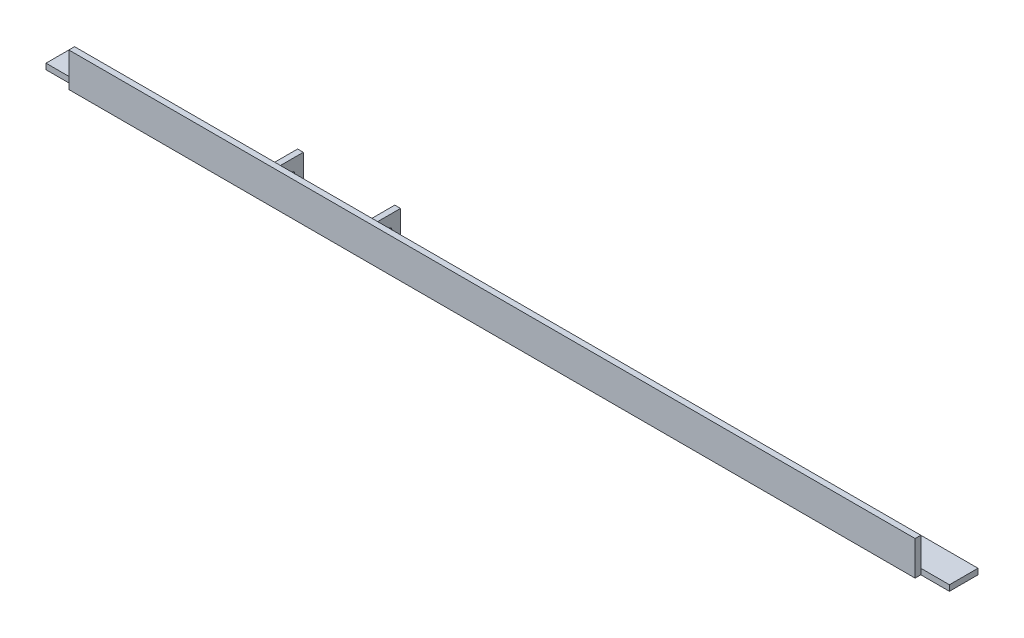
SolidWorks part; units mm, degrees
ref_plane "Front Plane" through (0, 0, 0) normal (0, 0, 1) x (1, 0, 0)
ref_plane "Top Plane" through (0, 0, 0) normal (0, 1, 0) x (1, 0, 0)
ref_plane "Right Plane" through (0, 0, 0) normal (1, 0, 0) x (0, 0, -1)
sketch "Sketch1" plane through (0, 0, 0) normal (1, 0, 0) x (0, 0, -1)
  line L0 (0, 0) -> (0, 31.75)
  line L1 (0, 31.75) -> (-6.35, 31.75)
  line L2 (-6.35, 31.75) -> (-6.35, -6.35)
  line L3 (-6.35, -6.35) -> (0, 0) construction
  line L4 (31.75, -6.35) -> (-6.35, -6.35)
  line L5 (31.75, 0) -> (31.75, -6.35)
  line L6 (0, 0) -> (31.75, 0)
  dimension "D1" = 45
  dimension "D2" = 38.1
  dimension "D3" = 6.35
extrude "Boss-Extrude1" add sketch "Sketch1" along normal blind 1003.3
sketch "Sketch2" plane through (0, 0, 0) normal (0, 1, 0) x (1, 0, 0)
  line L1 (254, 0) -> (355.6, 0) construction
  line L2 (254, 0) -> (254, 55.5106) construction
  line L3 (254, 55.5106) -> (355.6, 55.5106) construction
  line L4 (355.6, 0) -> (355.6, 55.5106) construction
  line L5 (1003.3, 31.75) -> (0, 31.75) construction
  line L6 (247.65, 31.75) -> (254, 31.75)
  line L7 (247.65, 31.75) -> (247.65, 6.35)
  line L9 (254, 31.75) -> (254, 0)
  line L10 (1003.3, 0) -> (0, 0) construction
  line L11 (247.65, 6.35) -> (254, 0) construction
  line L12 (222.25, 0) -> (254, 0)
  line L13 (222.25, 6.35) -> (247.65, 6.35)
  line L14 (222.25, 6.35) -> (222.25, 0)
  line L15 (0, 31.75) -> (0, 0) construction
  line L16 (304.8, 55.5106) -> (304.8, 0) construction
  line L17 (361.95, 6.35) -> (355.6, 0) construction
  line L18 (387.35, 6.35) -> (387.35, 0)
  line L19 (387.35, 6.35) -> (361.95, 6.35)
  line L20 (387.35, 0) -> (355.6, 0)
  line L21 (355.6, 31.75) -> (355.6, 0)
  line L22 (361.95, 31.75) -> (361.95, 6.35)
  line L23 (361.95, 31.75) -> (355.6, 31.75)
  dimension "D1" = 101.6
  dimension "D2" = 6.35
  dimension "D3" = 45
  dimension "D4" = 254
extrude "Boss-Extrude2" add sketch "Sketch2" along normal blind 25.4
sketch "Sketch3" plane through (0, 0, 0) normal (0, 1, 0) x (1, 0, 0)
  line L0 (355.6, 31.75) -> (355.6, 0) construction
  line L1 (254, 31.75) -> (355.6, 31.75)
  line L2 (254, 31.75) -> (254, 12.7)
  line L3 (254, 12.7) -> (355.6, 12.7)
  line L4 (355.6, 31.75) -> (355.6, 12.7)
  dimension "D1" = 19.05
extrude "Cut-Extrude1" cut sketch "Sketch3" against normal through all
sketch "Sketch4" plane through (247.65, 0, 0) normal (-1, 0, 0) x (0, 0, 1)
  line L0 (-31.75, 9.525) -> (-19.05, 9.525) construction
  line L1 (-31.75, 25.4) -> (-31.75, 0) construction
  line L2 (-19.05, 9.525) -> (-19.05, 0) construction
  line L3 (-31.75, 0) -> (0, 0) construction
  circle A0 centre (-19.05, 9.525) radius 3.175
  dimension "D1" = 6.35
  dimension "D2" = 9.525
  dimension "D3" = 12.7
extrude "Cut-Extrude2" cut sketch "Sketch4" against normal through all
sketch "Sketch5" plane through (0, 0, 6.35) normal (0, 0, 1) x (1, 0, 0)
  line L0 (1003.3, -6.35) -> (0, -6.35) construction
  line L1 (0, 31.75) -> (31.75, 31.75)
  line L2 (0, 31.75) -> (0, -6.35)
  line L3 (0, -6.35) -> (31.75, -6.35)
  line L4 (31.75, 31.75) -> (31.75, -6.35)
  line L5 (1003.3, 31.75) -> (0, 31.75) construction
  line L6 (1003.3, -6.35) -> (971.55, -6.35)
  line L7 (1003.3, -6.35) -> (1003.3, 31.75)
  line L8 (1003.3, 31.75) -> (971.55, 31.75)
  line L9 (971.55, -6.35) -> (971.55, 31.75)
  dimension "D1" = 31.75
extrude "Cut-Extrude3" cut sketch "Sketch5" against normal blind 6.35
